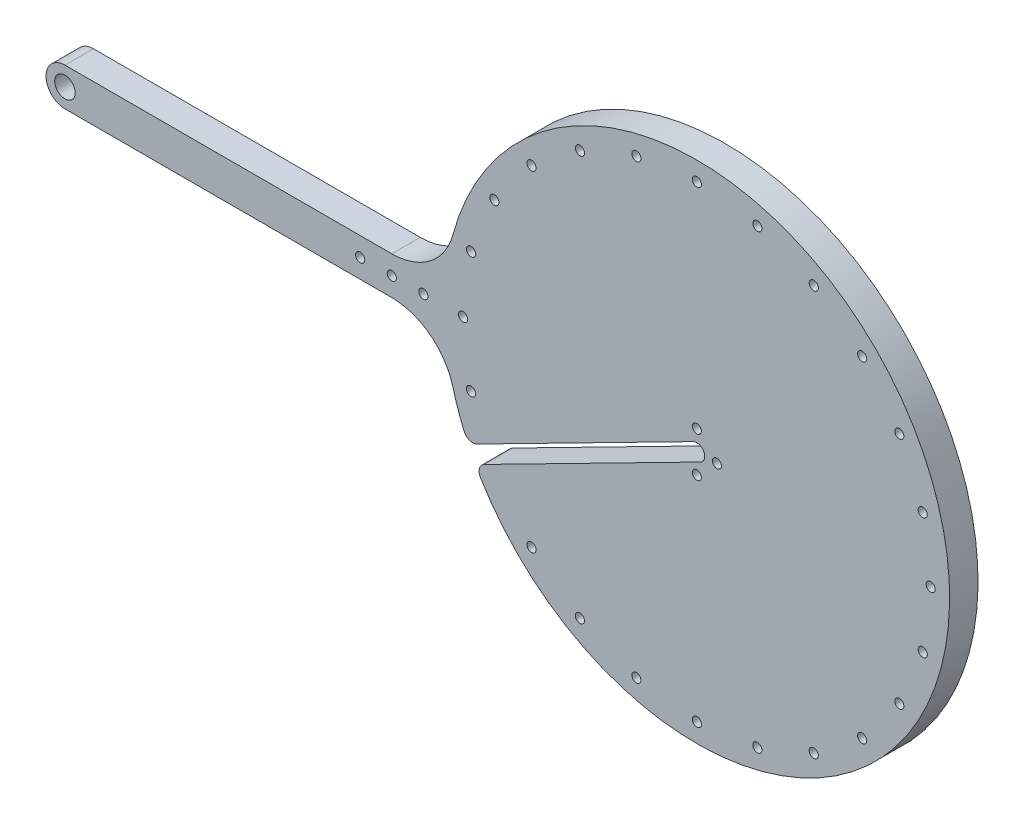
SolidWorks part; units mm, degrees
ref_plane "Front Plane" through (0, 0, 0) normal (0, 0, 1) x (1, 0, 0)
ref_plane "Top Plane" through (0, 0, 0) normal (0, 1, 0) x (1, 0, 0)
ref_plane "Right Plane" through (0, 0, 0) normal (1, 0, 0) x (0, 0, -1)
sketch "Sketch1" plane through (0, 0, 0) normal (0, 0, 1) x (1, 0, 0)
  line L0 (-155.3529, 10.2117) -> (-51.9137, 10.2117)
  line L1 (-51.9137, 22.2117) -> (-51.9137, 10.2117) construction
  line L2 (43.5118, 18.4391) -> (-27.7292, -17.8716)
  line L3 (45.7824, 13.9843) -> (-25.4587, -22.3263)
  line L5 (-51.9137, 22.2117) -> (-155.3529, 22.2117)
  arc A0 (-32.6016, -4.5883) -> (-51.9137, 10.2117) centre (-51.9137, -9.7883) ccw
  circle A1 centre (44.6471, 22.5617) radius 1.4225
  circle A2 centre (-26.8314, -2.9409) radius 1.45
  arc A3 (-51.9137, 22.2117) -> (-32.6016, 37.0117) centre (-51.9137, 42.2117) ccw
  arc A4 (-155.3529, 22.2117) -> (-155.3529, 10.2117) centre (-155.3529, 16.2117) ccw
  circle A5 centre (-155.3529, 16.2117) radius 3.25
  circle A6 centre (-26.8314, 35.3643) radius 1.45
  circle A7 centre (-19.4388, 53.2117) radius 1.45
  circle A8 centre (-29.3529, 16.2117) radius 1.45
  circle A9 centre (-51.9137, 16.2117) radius 1.45
  circle A10 centre (-41.9137, 16.2117) radius 1.45
  circle A11 centre (-61.9137, 16.2117) radius 1.45
  circle A12 centre (50.9971, 16.2117) radius 1.4225
  circle A13 centre (44.6471, 9.8617) radius 1.4225
  circle A14 centre (116.1256, -2.9409) radius 1.45
  circle A15 centre (108.733, -20.7883) radius 1.45
  circle A16 centre (96.973, -36.1142) radius 1.45
  circle A17 centre (81.6471, -47.8742) radius 1.45
  circle A18 centre (63.7997, -55.2668) radius 1.45
  circle A19 centre (44.6471, -57.7883) radius 1.45
  circle A20 centre (25.4945, -55.2668) radius 1.45
  circle A21 centre (7.6471, -47.8742) radius 1.45
  circle A22 centre (-7.6788, -36.1142) radius 1.45
  arc A23 (124.5879, 13.1348) -> (-32.6016, 37.0117) centre (44.6471, 16.2117) ccw
  arc A24 (-32.6016, -4.5883) -> (-27.7292, -17.8716) centre (44.6471, 16.2117) ccw
  arc A25 (-25.4587, -22.3263) -> (124.5879, 13.1348) centre (44.6471, 16.2117) ccw
  arc A33 (45.7824, 13.9843) -> (43.5118, 18.4391) centre (44.6471, 16.2117) ccw
  circle A34 centre (-7.6788, 68.5376) radius 1.45
  circle A35 centre (7.6471, 80.2976) radius 1.45
  circle A36 centre (25.4945, 87.6902) radius 1.45
  circle A37 centre (44.6471, 90.2117) radius 1.45
  circle A38 centre (63.7997, 87.6902) radius 1.45
  circle A39 centre (81.6471, 80.2976) radius 1.45
  circle A40 centre (96.973, 68.5376) radius 1.45
  circle A41 centre (108.733, 53.2117) radius 1.45
  circle A42 centre (116.1256, 35.3643) radius 1.45
  circle A44 centre (118.6471, 16.2117) radius 1.45
  dimension "D1" = 5
  dimension "D2" = 10
  dimension "D3" = 6.35
  dimension "D4" = 2.845
  dimension "D5" = 2.845
  dimension "D7" = 2.845
  dimension "D9" = 2.9
  dimension "D6" = 6.35
  dimension "D8" = 6.35
  dimension "D10" = 74
  dimension "D11" = 37
  dimension "D12" = 15
  dimension "D16" = 15
  dimension "D17" = 15
extrude "Boss-Extrude2" add sketch "Sketch1" along normal blind 9
fillet "Fillet1" radius 3 1 edges at (-27.7292, -17.8716, 4.5)
fillet "Fillet2" radius 3 1 edges at (-25.4587, -22.3263, 4.5)
